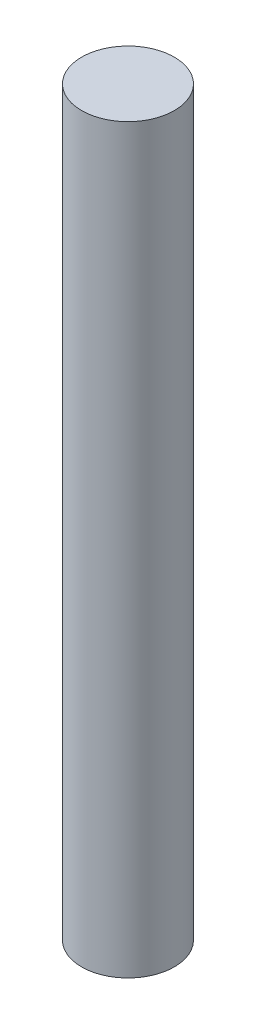
SolidWorks part; units mm, degrees
ref_plane "Front Plane" through (0, 0, 0) normal (0, 0, 1) x (1, 0, 0)
ref_plane "Top Plane" through (0, 0, 0) normal (0, 1, 0) x (1, 0, 0)
ref_plane "Right Plane" through (0, 0, 0) normal (1, 0, 0) x (0, 0, -1)
sketch "Sketch1" plane through (0, 0, 0) normal (0, 1, 0) x (1, 0, 0)
  circle A0 centre (0, 0) radius 3
  dimension "D1" = 6
extrude "Boss-Extrude1" add sketch "Sketch1" along normal blind 48
